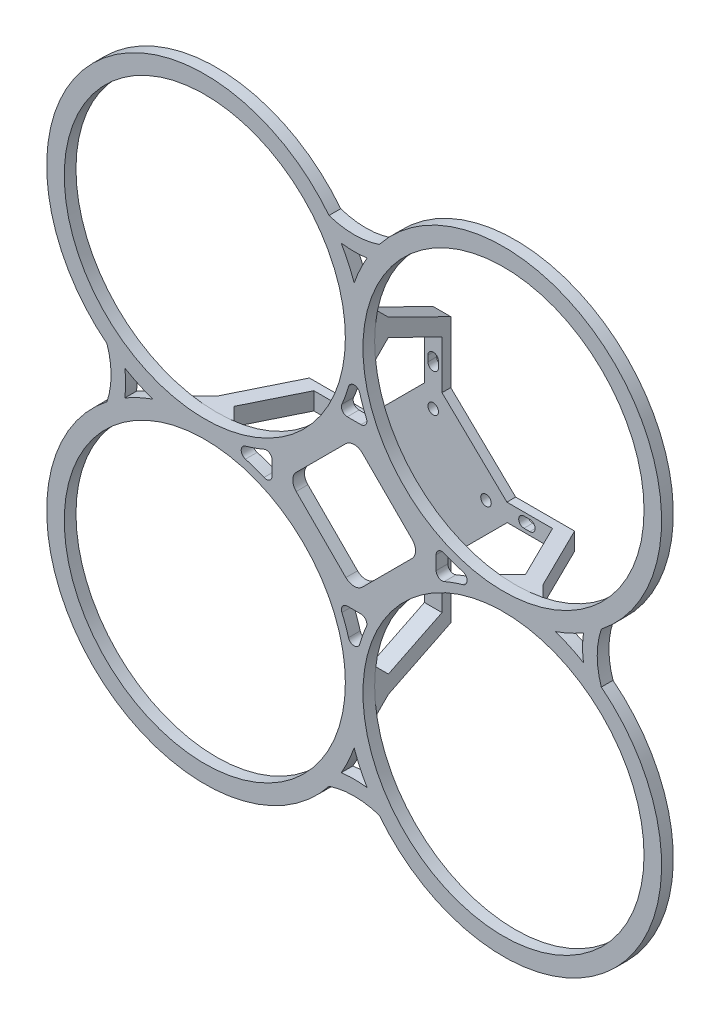
SolidWorks part; units mm, degrees
ref_plane "前视基准面" through (0, 0, 0) normal (0, 0, 1) x (1, 0, 0)
ref_plane "上视基准面" through (0, 0, 0) normal (0, 1, 0) x (1, 0, 0)
ref_plane "右视基准面" through (0, 0, 0) normal (1, 0, 0) x (0, 0, -1)
sketch "草图1" plane through (0, 0, 0) normal (0, 0, 1) x (1, 0, 0)
  line L1 (-51, -51) -> (51, -51) construction
  line L3 (-51, 51) -> (51, 51) construction
  line L20 (0, -18.0312) -> (18.0312, 0)
  line L23 (0, -18.0312) -> (-18.0312, 0)
  line L26 (-18.0312, 0) -> (0, 18.0312)
  line L27 (18.0312, 0) -> (0, 18.0312)
  line L28 (0, -9.8995) -> (9.8995, 0)
  line L31 (0, -9.8995) -> (-9.8995, 0)
  line L34 (-9.8995, 0) -> (0, 9.8995)
  line L37 (9.8995, 0) -> (0, 9.8995)
  line L40 (55, 0) -> (-55, 0) construction
  line L43 (0, -55) -> (0, 55) construction
  line L54 (0, 0) -> (148.7471, 0) construction
  line L57 (0, 0) -> (0, -150.6889) construction
  line L69 (-2.3379, 28) -> (2.3379, 28)
  line L73 (28, 2.3379) -> (28, -2.3379)
  line L74 (2.3379, -28) -> (-2.3379, -28)
  line L75 (-28, -2.3379) -> (-28, 2.3379)
  line L76 (-51, 51) -> (51, -51) construction
  line L77 (-36.9462, 0) -> (0, 36.9462) construction
  line L82 (-36.9462, 0) -> (30.9361, 0) construction
  circle A1 centre (-51, 51) radius 46
  arc A5 (0, 51) -> (-51, 0) centre (-51, 51) ccw
  arc A6 (-51, 0) -> (0, -51) centre (-51, -51) ccw
  arc A7 (0, -51) -> (51, 0) centre (51, -51) ccw
  arc A8 (51, 0) -> (0, 51) centre (51, 51) ccw
  circle A42 centre (0, 18.0312) radius 1.8
  circle A43 centre (-18.0312, 0) radius 1.8
  circle A44 centre (0, -18.0312) radius 1.8
  circle A45 centre (18.0312, 0) radius 1.8
  arc A65 (-89.5833, -17.6484) -> (-89.5833, 17.6484) centre (-110, 0) ccw
  arc A66 (-97.1495, -29.2924) -> (-97.1495, 29.2924) centre (-110, 0) ccw
  arc A67 (-17.6484, 89.5833) -> (17.6484, 89.5833) centre (0, 110) ccw
  arc A68 (-29.2924, 97.1495) -> (29.2924, 97.1495) centre (0, 110) ccw
  arc A69 (89.5833, 17.6484) -> (89.5833, -17.6484) centre (110, 0) ccw
  arc A70 (97.1495, 29.2924) -> (97.1495, -29.2924) centre (110, 0) ccw
  arc A71 (17.6484, -89.5833) -> (-17.6484, -89.5833) centre (0, -110) ccw
  arc A72 (29.2924, -97.1495) -> (-29.2924, -97.1495) centre (0, -110) ccw
  arc A80 (-1.9245, 37.122) -> (-4.1742, 30.7925) centre (-51, 51) cw
  arc A81 (1.9245, 37.122) -> (4.1742, 30.7925) centre (51, 51) ccw
  arc A88 (2.3379, 28) -> (4.1742, 30.7925) centre (2.3379, 30) ccw
  arc A89 (-2.3379, 28) -> (-4.1742, 30.7925) centre (-2.3379, 30) cw
  arc A90 (1.9245, 37.122) -> (-1.9245, 37.122) centre (0, 36.5778) ccw
  arc A91 (37.122, 1.9245) -> (30.7925, 4.1742) centre (51, 51) cw
  arc A92 (37.122, -1.9245) -> (37.122, 1.9245) centre (36.5778, 0) ccw
  arc A93 (28, 2.3379) -> (30.7925, 4.1742) centre (30, 2.3379) cw
  arc A94 (28, -2.3379) -> (30.7925, -4.1742) centre (30, -2.3379) ccw
  arc A95 (37.122, -1.9245) -> (30.7925, -4.1742) centre (51, -51) ccw
  arc A96 (1.9245, -37.122) -> (4.1742, -30.7925) centre (51, -51) cw
  arc A97 (-1.9245, -37.122) -> (1.9245, -37.122) centre (0, -36.5778) ccw
  arc A98 (2.3379, -28) -> (4.1742, -30.7925) centre (2.3379, -30) cw
  arc A99 (-2.3379, -28) -> (-4.1742, -30.7925) centre (-2.3379, -30) ccw
  arc A100 (-1.9245, -37.122) -> (-4.1742, -30.7925) centre (-51, -51) ccw
  arc A101 (-37.122, -1.9245) -> (-30.7925, -4.1742) centre (-51, -51) cw
  arc A102 (-37.122, 1.9245) -> (-37.122, -1.9245) centre (-36.5778, 0) ccw
  arc A103 (-28, -2.3379) -> (-30.7925, -4.1742) centre (-30, -2.3379) cw
  arc A104 (-28, 2.3379) -> (-30.7925, 4.1742) centre (-30, 2.3379) ccw
  arc A105 (-37.122, 1.9245) -> (-30.7925, 4.1742) centre (-51, 51) ccw
  circle A108 centre (51, 51) radius 46
  circle A109 centre (51, -51) radius 46
  circle A110 centre (-51, -51) radius 46
  point P0 (-51, -51)
  point P2 (51, 51)
  point P11 (-130, -130)
  point P12 (20, 0)
  point P13 (0, 18)
  point P104 (0, 0)
  point P113 (0, 0)
  point P122 (-87.0624, 87.0624)
  point P131 (0, 0)
  point P157 (0, 0)
  point P158 (87.0624, -87.0624)
  dimension "D1" = 4
  dimension "D2" = 45
  dimension "D3" = 2
  dimension "D5" = 92
  dimension "D4" = 4
extrude "凸台-拉伸1" add sketch "草图1" along normal blind 4
ref_plane "基准面1" through (0, 0, -26) normal (0, 0, 1) x (1, 0, 0)
sketch "草图4" plane through (0, 0, -26) normal (0, 0, 1) x (1, 0, 0)
  line L1 (-27.1796, 0) -> (0, 27.1796)
  line L2 (-27.1796, 0) -> (0, -28.2843)
  line L3 (0, -28.2843) -> (28.2843, 0)
  line L4 (0, 27.1796) -> (28.2843, 0)
  line L5 (-27.1796, 0) -> (28.2843, 0) construction
  line L6 (0, -28.2843) -> (0, 27.1796) construction
  circle A0 centre (0, 18.0312) radius 1.8 construction
  circle A1 centre (0, 18.0312) radius 1.8
  circle A2 centre (18.0312, 0) radius 1.8 construction
  circle A3 centre (0, -18.0312) radius 1.8 construction
  circle A4 centre (-18.0312, 0) radius 1.8 construction
  circle A5 centre (18.0312, 0) radius 1.8
  circle A6 centre (0, -18.0312) radius 1.8
  circle A7 centre (-18.0312, 0) radius 1.8
  point P12 (0, 0)
  dimension "D1" = 40
  dimension "D2" = 25.5
extrude "凸台-拉伸2" add sketch "草图4" along normal blind 3 separate body
sketch "草图8" plane through (0, 0, 0) normal (1, 0, 0) x (0, 0, -1)
  line L0 (23, 0) -> (23, 27.1796) construction
  line L1 (23, 0) -> (23, 20.4503) construction
  line L3 (23, 20.4503) -> (23, 40.7574)
  line L4 (23, 40.7574) -> (4.6929, 49.7761) construction
  line L7 (26, 43.2795) -> (26, 20.4503)
  line L8 (23, 20.4503) -> (26, 20.4503)
  line L10 (4.6929, 49.7761) -> (0, 45.0832)
  line L11 (4.6929, 49.7761) -> (23, 40.7574)
  line L13 (0, 17.6484) -> (0, 102) construction
  line L14 (0, 60.469) -> (0, 45.0832)
  line L15 (4.6929, 55.7761) -> (0, 60.469)
  line L16 (4.6929, 55.7761) -> (26, 45.2795)
  line L17 (26, 45.2795) -> (26, 43.2795)
  dimension "D1" = 3
extrude "凸台-拉伸3" add sketch "草图8" along normal mid plane 6
sketch "草图9" plane through (0, 0, -23) normal (0, 0, 1) x (1, 0, 0)
  line L4 (28.2843, 0) -> (0, 27.1796)
  line L5 (0, 27.1796) -> (-27.1796, 0)
  line L6 (-27.1796, 0) -> (0, -28.2843)
  line L7 (0, -28.2843) -> (28.2843, 0)
  line L8 (28.2843, 0) -> (0, 27.1796)
  line L9 (0, 27.1796) -> (-27.1796, 0)
  line L10 (-27.1796, 0) -> (0, -28.2843)
  line L11 (0, -28.2843) -> (28.2843, 0)
  dimension "D1" = 0
sketch "草图10" plane through (0, 0, 0) normal (0, 1, 0) x (1, 0, 0)
  line L0 (0, 0) -> (0, 50.3541)
pattern_circular "阵列(圆周)1" count 4 over 360 about axis through (0, 0, 0) along (0, 0, 1) of "凸台-拉伸3"
sketch "草图12" plane through (0, 0, -23) normal (0, 0, 1) x (1, 0, 0)
  line L0 (29.8948, 0) -> (-29.8948, 0) construction
  line L1 (0, 22.6274) -> (-22.6274, 0) construction
  line L2 (0, 22.6274) -> (22.6274, 0) construction
  line L3 (22.6274, 0) -> (0, -22.6274) construction
  line L4 (-22.6274, 0) -> (0, -22.6274) construction
  line L5 (0, 22.6274) -> (0, -22.6274) construction
  line L6 (22.6274, 0) -> (-22.6274, 0) construction
  line L7 (-19.799, -2.8284) -> (-2.8284, -19.799)
  line L8 (2.8284, -19.799) -> (19.799, -2.8284)
  line L9 (19.799, 2.8284) -> (2.8284, 19.799)
  line L10 (-2.8284, 19.799) -> (-19.799, 2.8284)
  arc A0 (19.799, 2.8284) -> (19.799, -2.8284) centre (16.9706, 0) cw
  arc A1 (2.8284, 19.799) -> (-2.8284, 19.799) centre (0, 16.9706) ccw
  arc A2 (-2.8284, -19.799) -> (2.8284, -19.799) centre (0, -16.9706) ccw
  arc A3 (-19.799, -2.8284) -> (-19.799, 2.8284) centre (-16.9706, 0) cw
  point P0 (0, 0)
  dimension "D2" = 4
  dimension "D1" = 32
extrude "切除-拉伸3" cut sketch "草图12" along normal mid plane 60
sketch "草图13" plane through (0, 0, -26) normal (0, 0, -1) x (-1, 0, 0)
  line L1 (0, 33) -> (0, 31) construction
  line L2 (0, 16.5) -> (0, -16.5) construction
  line L3 (1.8, 33) -> (1.8, 31)
  line L4 (-1.8, 33) -> (-1.8, 31)
  arc A1 (1.8, 33) -> (-1.8, 33) centre (0, 33) ccw
  arc A2 (-1.8, 31) -> (1.8, 31) centre (0, 31) ccw
  point P4 (0, 32)
  dimension "D1" = 1.8
  dimension "D2" = 2
  dimension "D3" = 32
extrude "切除-拉伸4" cut sketch "草图13" against normal up to next (3 mm away)
pattern_circular "阵列(圆周)2" count 4 over 360 about axis through (0, 0, 0) along (0, 0, 1) of "切除-拉伸4"
sketch "草图17" plane through (0, 3, 0) normal (0, 1, 0) x (1, 0, 0)
  line L6 (49.7761, 4.6929) -> (45.0832, 0)
  line L7 (45.2795, 26) -> (20.4503, 26)
  line L8 (20.4503, 26) -> (20.4503, 23)
  line L9 (20.4503, 23) -> (40.7574, 23)
  line L10 (40.7574, 23) -> (49.7761, 4.6929)
  line L11 (49.7761, 4.6929) -> (45.0832, 0)
  line L13 (45.2795, 26) -> (20.4503, 26)
  line L14 (20.4503, 26) -> (20.4503, 23)
  line L16 (40.7574, 23) -> (49.7761, 4.6929)
  line L22 (20.4503, 23) -> (40.7574, 23)
  line L24 (45.0832, 0) -> (60.469, 0)
  line L25 (45.0832, 0) -> (60.469, 0)
  line L29 (60.469, 0) -> (55.7761, 4.6929)
  line L30 (60.469, 0) -> (55.7761, 4.6929)
  line L31 (55.7761, 4.6929) -> (45.2795, 26)
  line L32 (55.7761, 4.6929) -> (45.2795, 26)
  dimension "D1" = 0
sketch "草图18" plane through (0, 0, -26) normal (0, 0, -1) x (-1, 0, 0)
  line L4 (0, 27.1796) -> (-28.2843, 0)
  line L5 (-28.2843, 0) -> (0, -28.2843)
  line L6 (0, -28.2843) -> (27.1796, 0)
  line L7 (27.1796, 0) -> (0, 27.1796)
  line L11 (22.1796, 5) -> (3, 24.1796)
  line L12 (3, 20.4503) -> (3, 45.2795)
  line L13 (3, 45.2795) -> (-3, 45.2795)
  line L14 (-3, 45.2795) -> (-3, 20.4503)
  line L15 (-3, 20.4503) -> (-1.9727, 20.4503)
  line L16 (3, 24.1796) -> (3, 45.2795)
  line L21 (1.9727, 20.4503) -> (3, 20.4503)
  line L22 (1.9727, 20.4503) -> (3, 20.4503)
  line L29 (3, 45.2795) -> (-3, 45.2795)
  arc A1 (1.9727, 20.4503) -> (-1.9727, 20.4503) centre (0, 16.9706) ccw
  arc A2 (1.9727, 20.4503) -> (-1.9727, 20.4503) centre (0, 16.9706) ccw
  dimension "D1" = 0
  dimension "D2" = 0
ref_plane "基准面2" through (0, 0, -3) normal (0, 0, 1) x (1, 0, 0)
ref_plane "基准面3" through (0, 0, 4) normal (0, 0, 1) x (1, 0, 0)
sketch "草图21" plane through (0, 0, 4) normal (0, 0, 1) x (1, 0, 0)
  line L0 (-825.3754, 825.3754) -> (-89.6611, 89.6611) construction
  line L1 (-90.5097, 90.5097) -> (-89.6611, 89.6611) construction
  line L4 (-88.5298, 92.4896) -> (-85.0282, 88.988)
  line L5 (-92.4896, 88.5298) -> (-88.988, 85.0282)
  line L6 (-92.4896, 88.5298) -> (-87.4628, 83.503) construction
  line L7 (-83.503, 83.503) -> (-0.1118, 0.1118) construction
  line L8 (-91.3582, 89.6611) -> (-86.3314, 84.6343) construction
  line L9 (-89.6611, 91.3582) -> (-84.6343, 86.3314) construction
  line L10 (-88.5298, 92.4896) -> (-83.503, 87.4628) construction
  line L12 (-87.0624, 87.0624) -> (-85.4829, 85.4829) construction
  arc A0 (-87.4628, 83.503) -> (-83.503, 87.4628) centre (-85.4829, 85.4829) ccw construction
  arc A1 (-17.6484, 89.5833) -> (-89.5833, 17.6484) centre (-51, 51) ccw construction
  arc A2 (-17.6484, 89.5833) -> (-89.5833, 17.6484) centre (-51, 51) ccw construction
  arc A3 (-89.6611, 91.3582) -> (-91.3582, 89.6611) centre (-90.5097, 90.5097) ccw
  arc A6 (-88.5298, 92.4896) -> (-92.4896, 88.5298) centre (-90.5097, 90.5097) ccw
  arc A7 (-86.3314, 84.6343) -> (-84.6343, 86.3314) centre (-85.4829, 85.4829) ccw construction
  circle A8 centre (-90.5097, 90.5097) radius 1.2
  arc A9 (-88.988, 85.0282) -> (-85.0282, 88.988) centre (-51, 51) cw
  dimension "D1" = 1.2
  dimension "D3" = 128
  dimension "D2" = 1.6
sketch "草图22" plane through (-3, 0, 0) normal (-1, 0, 0) x (0, 0, 1)
  line L2 (-26, 27.1796) -> (-26, 24.1796)
  line L3 (-26, 24.1796) -> (-23, 24.1796)
  line L4 (-26, 27.1796) -> (-26, 0)
  line L5 (-26, 0) -> (-23, 0)
  line L6 (-23, 0) -> (-23, 27.1796)
  line L7 (-23, 27.1796) -> (-26, 27.1796)
  line L11 (-23, 27.1796) -> (-26, 27.1796)
  line L12 (-23, 24.1796) -> (-23, 27.1796)
  dimension "D1" = 0
extrude "凸台-拉伸6" add sketch "草图22" against normal blind 1
pattern_circular "阵列(圆周)8" count 4 over 360 about axis through (0, 0, 0) along (0, 0, -1) of "凸台-拉伸6"
sketch "草图23" plane through (0, 0, 4) normal (0, 0, 1) x (1, 0, 0)
  line L0 (19.799, -2.8284) -> (2.8284, -19.799) construction
  line L1 (2.8284, 19.799) -> (19.799, 2.8284) construction
  line L2 (-19.799, 2.8284) -> (-2.8284, 19.799) construction
  line L3 (-2.8284, -19.799) -> (-19.799, -2.8284) construction
  line L4 (19.799, -2.8284) -> (2.8284, -19.799)
  line L5 (2.8284, 19.799) -> (19.799, 2.8284)
  line L6 (-19.799, 2.8284) -> (-2.8284, 19.799)
  line L7 (-2.8284, -19.799) -> (-19.799, -2.8284)
  arc A0 (-2.8284, -19.799) -> (2.8284, -19.799) centre (0, -16.9706) ccw construction
  arc A1 (19.799, -2.8284) -> (19.799, 2.8284) centre (16.9706, 0) ccw construction
  arc A2 (2.8284, 19.799) -> (-2.8284, 19.799) centre (0, 16.9706) ccw construction
  arc A3 (-19.799, 2.8284) -> (-19.799, -2.8284) centre (-16.9706, 0) ccw construction
  arc A4 (-2.8284, -19.799) -> (2.8284, -19.799) centre (0, -16.9706) ccw
  arc A5 (19.799, -2.8284) -> (19.799, 2.8284) centre (16.9706, 0) ccw
  arc A6 (2.8284, 19.799) -> (-2.8284, 19.799) centre (0, 16.9706) ccw
  arc A7 (-19.799, 2.8284) -> (-19.799, -2.8284) centre (-16.9706, 0) ccw
sketch "草图24" plane through (0, 0, 4) normal (0, 0, 1) x (1, 0, 0)
  line L0 (-5, 51) -> (5, 51)
  line L1 (51, 5) -> (51, -5)
  line L2 (5, -51) -> (-5, -51)
  line L3 (-51, -5) -> (-51, 5)
  arc A2 (-68.7482, 0) -> (0, -68.7482) centre (-51, -51) ccw
  arc A5 (51, 5) -> (5, 51) centre (51, 51) ccw
  arc A6 (5, -51) -> (51, -5) centre (51, -51) ccw
  arc A7 (-51, -5) -> (-5, -51) centre (-51, -51) ccw
  arc A8 (-5, 51) -> (-51, 5) centre (-51, 51) ccw
  arc A9 (0, 68.7482) -> (-68.7482, 0) centre (-51, 51) ccw
  arc A10 (68.7482, 0) -> (0, 68.7482) centre (51, 51) ccw
  arc A11 (0, -68.7482) -> (68.7482, 0) centre (51, -51) ccw
  point P12 (0, 0)
  point P20 (0, 0)
  dimension "D2" = 4
extrude "凸台-拉伸7" add sketch "草图24" against normal blind 4
sketch "草图25" plane through (0, 0, 4) normal (0, 0, 1) x (1, 0, 0)
  circle A0 centre (51, 51) radius 48
  circle A1 centre (51, -51) radius 48
  circle A2 centre (-51, -51) radius 48
  circle A3 centre (-51, 51) radius 48
  point P12 (0, 0)
  dimension "D1" = 4
extrude "切除-拉伸5" cut sketch "草图25" against normal blind 4
